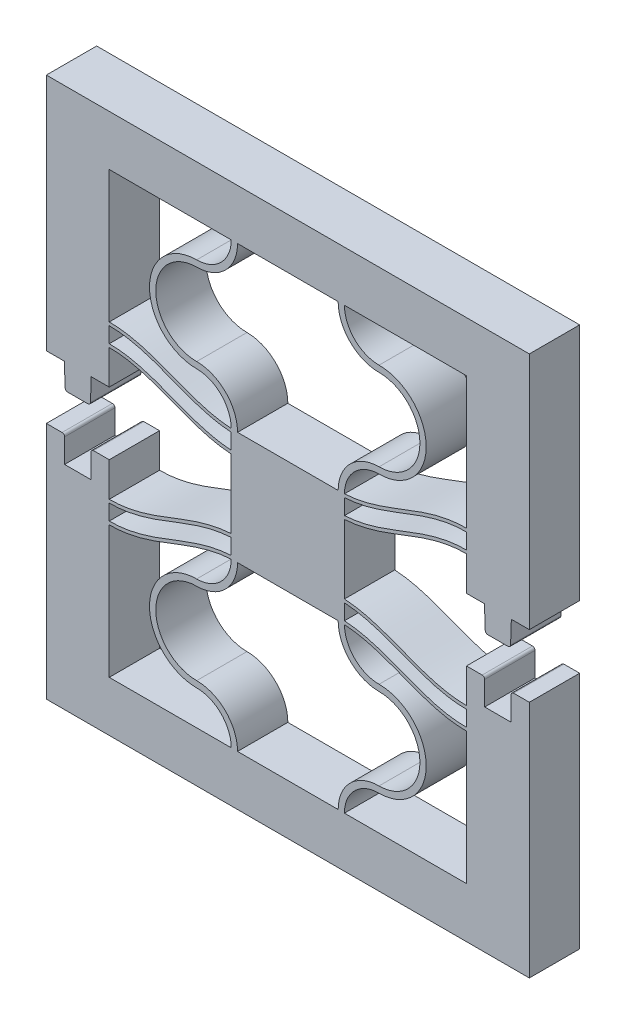
SolidWorks part; units mm, degrees
ref_plane "Front Plane" through (0, 0, 0) normal (0, 0, 1) x (1, 0, 0)
ref_plane "Top Plane" through (0, 0, 0) normal (0, 1, 0) x (1, 0, 0)
ref_plane "Right Plane" through (0, 0, 0) normal (1, 0, 0) x (0, 0, -1)
sketch "Sketch1" plane through (0, 0, 0) normal (0, 0, 1) x (1, 0, 0)
  line L4 (0, 10.5) -> (0, 0)
  line L5 (10.2, 0) -> (10.2, 13) construction
  line L6 (10.2, 13) -> (10.2, 15.9852) construction
  line L17 (9.7, 0) -> (0, 0)
  line L18 (10.7, 0) -> (20.4, 0)
  line L19 (20.4, 0) -> (20.4, 10.5)
  line L20 (10.7, 13.2452) -> (10.7, 14.4852)
  line L21 (9.7, 13.2452) -> (9.7, 14.4852)
  line L22 (10.7, 14.7452) -> (10.7, 15.9852)
  line L23 (10.7, 15.9852) -> (9.7, 15.9852)
  line L24 (9.7, 15.9852) -> (9.7, 14.7452)
  line L31 (-5, 12.26) -> (-5, -4)
  line L32 (-5, -4) -> (25.4, -4)
  line L33 (25.4, -4) -> (25.4, 12.26)
  line L34 (0, 10.76) -> (0, 12)
  line L36 (-5, 12.26) -> (0, 12.26)
  line L37 (25.4, 12.26) -> (20.4, 12.26)
  line L38 (20.4, 10.76) -> (20.4, 12)
  arc A0 (10.2, 13) -> (6.95, 9.75) centre (6.95, 13) cw
  arc A1 (6.95, 9.75) -> (6.95, 3.25) centre (6.95, 6.5) ccw
  arc A2 (6.95, 3.25) -> (10.2, 0) centre (6.95, 0) cw
  arc A3 (9.7, 12.9852) -> (6.95, 10.25) centre (6.95, 13) cw
  arc A4 (6.95, 10.25) -> (6.95, 2.75) centre (6.95, 6.5) ccw
  arc A5 (6.95, 2.75) -> (9.7, 0) centre (6.95, 0) cw
  arc A6 (9.7, 13) -> (6.95, 10.25) centre (6.95, 13) cw construction
  arc A7 (13.45, 3.25) -> (10.2, 0) centre (13.45, 0) ccw
  arc A8 (13.45, 2.75) -> (10.7, 0) centre (13.45, 0) ccw
  arc A9 (13.45, 9.75) -> (13.45, 3.25) centre (13.45, 6.5) cw
  arc A10 (13.45, 10.25) -> (13.45, 2.75) centre (13.45, 6.5) cw
  arc A11 (10.7, 12.9852) -> (13.45, 10.25) centre (13.45, 13) ccw
  arc A12 (10.2, 13) -> (13.45, 9.75) centre (13.45, 13) ccw
  spline S0 degree 4 poles (-2.0399, 10.9987) (-1.9769, 10.9844) (-1.8506, 10.9568) (-1.6594, 10.9185) (-1.4063, 10.8738) (-1.1473, 10.836) (-0.8994, 10.8056) (-0.6275, 10.7825) (-0.4084, 10.7671) (-0.0945, 10.7598) (0.0489, 10.7593) (0.3554, 10.7653) (0.5833, 10.7785) (0.8327, 10.7992) (1.1232, 10.8326) (1.4148, 10.8743) (1.7521, 10.9345) (2.2064, 11.0333) (2.726, 11.1697) (3.2397, 11.3281) (3.7479, 11.5024) (4.1845, 11.6613) (4.5513, 11.7992) (4.9172, 11.9395) (5.2828, 12.0805) (5.7402, 12.2559) (6.427, 12.5125) (7.2136, 12.7819) (8.1107, 13.0284) (9.0261, 13.1932) (9.8075, 13.2661) (10.5925, 13.2661) (11.3739, 13.1932) (12.2893, 13.0284) (13.1864, 12.7819) (13.973, 12.5125) (14.6598, 12.2559) (15.2087, 12.0455) (15.6656, 11.8688) (16.1235, 11.6948) (16.6521, 11.5024) (17.1603, 11.3281) (17.6739, 11.1697) (18.1937, 11.0333) (18.5999, 10.9449) (18.8889, 10.8915) (19.1309, 10.8534) (19.3251, 10.827) (19.5196, 10.8048) (19.7158, 10.7868) (19.909, 10.7733) (20.1017, 10.7642) (20.3513, 10.7593) (20.4943, 10.7598) (20.8085, 10.7671) (21.0274, 10.7825) (21.2994, 10.8056) (21.5473, 10.836) (21.8063, 10.8738) (22.0594, 10.9185) (22.2506, 10.9568) (22.3769, 10.9844) (22.4399, 10.9987) knots 0 0 0 0 0 0.010251 0.020502 0.030753 0.041005 0.05113 0.061255 0.071381 0.081506 0.089265 0.097024 0.112543 0.120302 0.128061 0.143579 0.159098 0.174616 0.201648 0.22868 0.244198 0.259716 0.275235 0.290753 0.306271 0.32179 0.352826 0.40689 0.437927 0.468963 0.5 0.531037 0.562073 0.59311 0.647174 0.67821 0.693729 0.709247 0.740284 0.755802 0.77132 0.798352 0.825384 0.840902 0.856421 0.86418 0.871939 0.879698 0.887457 0.895217 0.902976 0.910735 0.918494 0.928619 0.938745 0.94887 0.958995 0.969247 0.979498 0.989749 1 1 1 1 1 construction
  spline S1 degree 4 poles (0, 10.76) (0.041, 10.76) (0.1243, 10.7608) (0.3554, 10.7653) (0.5833, 10.7785) (0.8327, 10.7992) (1.1232, 10.8326) (1.4148, 10.8743) (1.7521, 10.9345) (2.2064, 11.0333) (2.726, 11.1697) (3.2397, 11.3281) (3.7479, 11.5024) (4.1845, 11.6613) (4.5513, 11.7992) (4.9172, 11.9395) (5.2828, 12.0805) (5.7402, 12.2559) (6.427, 12.5125) (7.2136, 12.7819) (8.1107, 13.0284) (9.0261, 13.1932) (9.8075, 13.2661) (10.5925, 13.2661) (11.3739, 13.1932) (12.2893, 13.0284) (13.1864, 12.7819) (13.973, 12.5125) (14.6598, 12.2559) (15.2087, 12.0455) (15.6656, 11.8688) (16.1235, 11.6948) (16.6521, 11.5024) (17.1603, 11.3281) (17.6739, 11.1697) (18.1937, 11.0333) (18.5999, 10.9449) (18.8889, 10.8915) (19.1309, 10.8534) (19.3251, 10.827) (19.5196, 10.8048) (19.7158, 10.7868) (19.909, 10.7733) (20.1017, 10.7642) (20.2757, 10.7608) (20.359, 10.76) (20.4, 10.76) knots 0.081506 0.081506 0.081506 0.081506 0.081506 0.089265 0.097024 0.112543 0.120302 0.128061 0.143579 0.159098 0.174616 0.201648 0.22868 0.244198 0.259716 0.275235 0.290753 0.306271 0.32179 0.352826 0.40689 0.437927 0.468963 0.5 0.531037 0.562073 0.59311 0.647174 0.67821 0.693729 0.709247 0.740284 0.755802 0.77132 0.798352 0.825384 0.840902 0.856421 0.86418 0.871939 0.879698 0.887457 0.895217 0.902976 0.910735 0.918494 0.918494 0.918494 0.918494 0.918494
  spline S2 degree 4 poles (-2.0399, 12.2387) (-1.9769, 12.2244) (-1.8506, 12.1968) (-1.6594, 12.1585) (-1.4063, 12.1138) (-1.1473, 12.076) (-0.8994, 12.0456) (-0.6275, 12.0225) (-0.4084, 12.0071) (-0.0945, 11.9998) (0.0489, 11.9993) (0.3554, 12.0053) (0.5833, 12.0185) (0.8327, 12.0392) (1.1232, 12.0726) (1.4148, 12.1143) (1.7521, 12.1745) (2.2064, 12.2733) (2.726, 12.4097) (3.2397, 12.5681) (3.7479, 12.7424) (4.1845, 12.9013) (4.5513, 13.0392) (4.9172, 13.1795) (5.2828, 13.3205) (5.7402, 13.4959) (6.427, 13.7525) (7.2136, 14.0219) (8.1107, 14.2684) (9.0261, 14.4332) (9.8075, 14.5061) (10.5925, 14.5061) (11.3739, 14.4332) (12.2893, 14.2684) (13.1864, 14.0219) (13.973, 13.7525) (14.6598, 13.4959) (15.2087, 13.2855) (15.6656, 13.1088) (16.1235, 12.9348) (16.6521, 12.7424) (17.1603, 12.5681) (17.6739, 12.4097) (18.1937, 12.2733) (18.5999, 12.1849) (18.8889, 12.1315) (19.1309, 12.0934) (19.3251, 12.067) (19.5196, 12.0448) (19.7158, 12.0268) (19.909, 12.0133) (20.1017, 12.0042) (20.3513, 11.9993) (20.4943, 11.9998) (20.8085, 12.0071) (21.0274, 12.0225) (21.2994, 12.0456) (21.5473, 12.076) (21.8063, 12.1138) (22.0594, 12.1585) (22.2506, 12.1968) (22.3769, 12.2244) (22.4399, 12.2387) knots 0 0 0 0 0 0.010251 0.020502 0.030753 0.041005 0.05113 0.061255 0.071381 0.081506 0.089265 0.097024 0.112543 0.120302 0.128061 0.143579 0.159098 0.174616 0.201648 0.22868 0.244198 0.259716 0.275235 0.290753 0.306271 0.32179 0.352826 0.40689 0.437927 0.468963 0.5 0.531037 0.562073 0.59311 0.647174 0.67821 0.693729 0.709247 0.740284 0.755802 0.77132 0.798352 0.825384 0.840902 0.856421 0.86418 0.871939 0.879698 0.887457 0.895217 0.902976 0.910735 0.918494 0.928619 0.938745 0.94887 0.958995 0.969247 0.979498 0.989749 1 1 1 1 1 construction
  spline S3 degree 4 poles (0, 12) (0.041, 12) (0.1243, 12.0008) (0.3554, 12.0053) (0.5833, 12.0185) (0.8327, 12.0392) (1.1232, 12.0726) (1.4148, 12.1143) (1.7521, 12.1745) (2.2064, 12.2733) (2.726, 12.4097) (3.2397, 12.5681) (3.7479, 12.7424) (4.1845, 12.9013) (4.5513, 13.0392) (4.9172, 13.1795) (5.2828, 13.3205) (5.7402, 13.4959) (6.427, 13.7525) (7.2136, 14.0219) (8.1107, 14.2684) (9.0261, 14.4332) (9.8075, 14.5061) (10.5925, 14.5061) (11.3739, 14.4332) (12.2893, 14.2684) (13.1864, 14.0219) (13.973, 13.7525) (14.6598, 13.4959) (15.2087, 13.2855) (15.6656, 13.1088) (16.1235, 12.9348) (16.6521, 12.7424) (17.1603, 12.5681) (17.6739, 12.4097) (18.1937, 12.2733) (18.5999, 12.1849) (18.8889, 12.1315) (19.1309, 12.0934) (19.3251, 12.067) (19.5196, 12.0448) (19.7158, 12.0268) (19.909, 12.0133) (20.1017, 12.0042) (20.2757, 12.0008) (20.359, 12) (20.4, 12) knots 0.081506 0.081506 0.081506 0.081506 0.081506 0.089265 0.097024 0.112543 0.120302 0.128061 0.143579 0.159098 0.174616 0.201648 0.22868 0.244198 0.259716 0.275235 0.290753 0.306271 0.32179 0.352826 0.40689 0.437927 0.468963 0.5 0.531037 0.562073 0.59311 0.647174 0.67821 0.693729 0.709247 0.740284 0.755802 0.77132 0.798352 0.825384 0.840902 0.856421 0.86418 0.871939 0.879698 0.887457 0.895217 0.902976 0.910735 0.918494 0.918494 0.918494 0.918494 0.918494
  spline S4 degree 4 poles (-2.0399, 12.4987) (-1.9769, 12.4844) (-1.8506, 12.4568) (-1.6594, 12.4185) (-1.4063, 12.3738) (-1.1473, 12.336) (-0.8994, 12.3056) (-0.6275, 12.2825) (-0.4084, 12.2671) (-0.0945, 12.2598) (0.0489, 12.2593) (0.3554, 12.2653) (0.5833, 12.2785) (0.8327, 12.2992) (1.1232, 12.3326) (1.4148, 12.3743) (1.7521, 12.4345) (2.2064, 12.5333) (2.726, 12.6697) (3.2397, 12.8281) (3.7479, 13.0024) (4.1845, 13.1613) (4.5513, 13.2992) (4.9172, 13.4395) (5.2828, 13.5805) (5.7402, 13.7559) (6.427, 14.0125) (7.2136, 14.2819) (8.1107, 14.5284) (9.0261, 14.6932) (9.8075, 14.7661) (10.5925, 14.7661) (11.3739, 14.6932) (12.2893, 14.5284) (13.1864, 14.2819) (13.973, 14.0125) (14.6598, 13.7559) (15.2087, 13.5455) (15.6656, 13.3688) (16.1235, 13.1948) (16.6521, 13.0024) (17.1603, 12.8281) (17.6739, 12.6697) (18.1937, 12.5333) (18.5999, 12.4449) (18.8889, 12.3915) (19.1309, 12.3534) (19.3251, 12.327) (19.5196, 12.3048) (19.7158, 12.2868) (19.909, 12.2733) (20.1017, 12.2642) (20.3513, 12.2593) (20.4943, 12.2598) (20.8085, 12.2671) (21.0274, 12.2825) (21.2994, 12.3056) (21.5473, 12.336) (21.8063, 12.3738) (22.0594, 12.4185) (22.2506, 12.4568) (22.3769, 12.4844) (22.4399, 12.4987) knots 0 0 0 0 0 0.010251 0.020502 0.030753 0.041005 0.05113 0.061255 0.071381 0.081506 0.089265 0.097024 0.112543 0.120302 0.128061 0.143579 0.159098 0.174616 0.201648 0.22868 0.244198 0.259716 0.275235 0.290753 0.306271 0.32179 0.352826 0.40689 0.437927 0.468963 0.5 0.531037 0.562073 0.59311 0.647174 0.67821 0.693729 0.709247 0.740284 0.755802 0.77132 0.798352 0.825384 0.840902 0.856421 0.86418 0.871939 0.879698 0.887457 0.895217 0.902976 0.910735 0.918494 0.928619 0.938745 0.94887 0.958995 0.969247 0.979498 0.989749 1 1 1 1 1 construction
  spline S5 degree 4 poles (0, 12.26) (0.041, 12.26) (0.1243, 12.2608) (0.3554, 12.2653) (0.5833, 12.2785) (0.8327, 12.2992) (1.1232, 12.3326) (1.4148, 12.3743) (1.7521, 12.4345) (2.2064, 12.5333) (2.726, 12.6697) (3.2397, 12.8281) (3.7479, 13.0024) (4.1845, 13.1613) (4.5513, 13.2992) (4.9172, 13.4395) (5.2828, 13.5805) (5.7402, 13.7559) (6.427, 14.0125) (7.2136, 14.2819) (8.1107, 14.5284) (9.0261, 14.6932) (9.8075, 14.7661) (10.5925, 14.7661) (11.3739, 14.6932) (12.2893, 14.5284) (13.1864, 14.2819) (13.973, 14.0125) (14.6598, 13.7559) (15.2087, 13.5455) (15.6656, 13.3688) (16.1235, 13.1948) (16.6521, 13.0024) (17.1603, 12.8281) (17.6739, 12.6697) (18.1937, 12.5333) (18.5999, 12.4449) (18.8889, 12.3915) (19.1309, 12.3534) (19.3251, 12.327) (19.5196, 12.3048) (19.7158, 12.2868) (19.909, 12.2733) (20.1017, 12.2642) (20.2757, 12.2608) (20.359, 12.26) (20.4, 12.26) knots 0.081506 0.081506 0.081506 0.081506 0.081506 0.089265 0.097024 0.112543 0.120302 0.128061 0.143579 0.159098 0.174616 0.201648 0.22868 0.244198 0.259716 0.275235 0.290753 0.306271 0.32179 0.352826 0.40689 0.437927 0.468963 0.5 0.531037 0.562073 0.59311 0.647174 0.67821 0.693729 0.709247 0.740284 0.755802 0.77132 0.798352 0.825384 0.840902 0.856421 0.86418 0.871939 0.879698 0.887457 0.895217 0.902976 0.910735 0.918494 0.918494 0.918494 0.918494 0.918494
  spline S8 degree 4 poles (-2.0399, 10.7387) (-1.9769, 10.7244) (-1.8506, 10.6968) (-1.6594, 10.6585) (-1.4063, 10.6138) (-1.1473, 10.576) (-0.8994, 10.5456) (-0.6275, 10.5225) (-0.4084, 10.5071) (-0.0945, 10.4998) (0.0489, 10.4993) (0.3554, 10.5053) (0.5833, 10.5185) (0.8327, 10.5392) (1.1232, 10.5726) (1.4148, 10.6143) (1.7521, 10.6745) (2.2064, 10.7733) (2.726, 10.9097) (3.2397, 11.0681) (3.7479, 11.2424) (4.1845, 11.4013) (4.5513, 11.5392) (4.9172, 11.6795) (5.2828, 11.8205) (5.7402, 11.9959) (6.427, 12.2525) (7.2136, 12.5219) (8.1107, 12.7684) (9.0261, 12.9332) (9.8075, 13.0061) (10.5925, 13.0061) (11.3739, 12.9332) (12.2893, 12.7684) (13.1864, 12.5219) (13.973, 12.2525) (14.6598, 11.9959) (15.2087, 11.7855) (15.6656, 11.6088) (16.1235, 11.4348) (16.6521, 11.2424) (17.1603, 11.0681) (17.6739, 10.9097) (18.1937, 10.7733) (18.5999, 10.6849) (18.8889, 10.6315) (19.1309, 10.5934) (19.3251, 10.567) (19.5196, 10.5448) (19.7158, 10.5268) (19.909, 10.5133) (20.1017, 10.5042) (20.3513, 10.4993) (20.4943, 10.4998) (20.8085, 10.5071) (21.0274, 10.5225) (21.2994, 10.5456) (21.5473, 10.576) (21.8063, 10.6138) (22.0594, 10.6585) (22.2506, 10.6968) (22.3769, 10.7244) (22.4399, 10.7387) knots 0 0 0 0 0 0.010251 0.020502 0.030753 0.041005 0.05113 0.061255 0.071381 0.081506 0.089265 0.097024 0.112543 0.120302 0.128061 0.143579 0.159098 0.174616 0.201648 0.22868 0.244198 0.259716 0.275235 0.290753 0.306271 0.32179 0.352826 0.40689 0.437927 0.468963 0.5 0.531037 0.562073 0.59311 0.647174 0.67821 0.693729 0.709247 0.740284 0.755802 0.77132 0.798352 0.825384 0.840902 0.856421 0.86418 0.871939 0.879698 0.887457 0.895217 0.902976 0.910735 0.918494 0.928619 0.938745 0.94887 0.958995 0.969247 0.979498 0.989749 1 1 1 1 1 construction
  spline S9 degree 4 poles (0, 10.5) (0.041, 10.5) (0.1243, 10.5008) (0.3554, 10.5053) (0.5833, 10.5185) (0.8327, 10.5392) (1.1232, 10.5726) (1.4148, 10.6143) (1.7521, 10.6745) (2.2064, 10.7733) (2.726, 10.9097) (3.2397, 11.0681) (3.7479, 11.2424) (4.1845, 11.4013) (4.5513, 11.5392) (4.9172, 11.6795) (5.2828, 11.8205) (5.7402, 11.9959) (6.427, 12.2525) (7.2136, 12.5219) (8.1107, 12.7684) (9.0261, 12.9332) (9.8075, 13.0061) (10.5925, 13.0061) (11.3739, 12.9332) (12.2893, 12.7684) (13.1864, 12.5219) (13.973, 12.2525) (14.6598, 11.9959) (15.2087, 11.7855) (15.6656, 11.6088) (16.1235, 11.4348) (16.6521, 11.2424) (17.1603, 11.0681) (17.6739, 10.9097) (18.1937, 10.7733) (18.5999, 10.6849) (18.8889, 10.6315) (19.1309, 10.5934) (19.3251, 10.567) (19.5196, 10.5448) (19.7158, 10.5268) (19.909, 10.5133) (20.1017, 10.5042) (20.2757, 10.5008) (20.359, 10.5) (20.4, 10.5) knots 0.081506 0.081506 0.081506 0.081506 0.081506 0.089265 0.097024 0.112543 0.120302 0.128061 0.143579 0.159098 0.174616 0.201648 0.22868 0.244198 0.259716 0.275235 0.290753 0.306271 0.32179 0.352826 0.40689 0.437927 0.468963 0.5 0.531037 0.562073 0.59311 0.647174 0.67821 0.693729 0.709247 0.740284 0.755802 0.77132 0.798352 0.825384 0.840902 0.856421 0.86418 0.871939 0.879698 0.887457 0.895217 0.902976 0.910735 0.918494 0.918494 0.918494 0.918494 0.918494
  dimension "D4" = 0.26
  dimension "D6" = 4
  dimension "D1" = 13
  dimension "D2" = 0.5
  dimension "D3" = 0.26
  dimension "D7" = 5
  dimension "D5" = 1.5
extrude "Boss-Extrude1" add sketch "Sketch1" along normal blind 4
sketch "Sketch4" plane through (0, 15.9852, 0) normal (0, 1, 0) x (1, 0, 0)
  line L24 (10.7, 0) -> (9.7, 0)
  line L25 (9.7, 0) -> (9.7, -4)
  line L26 (10.7, 0) -> (9.7, 0)
  line L27 (10.7, -4) -> (10.7, 0)
  line L29 (9.7, 0) -> (9.7, -4)
  line L31 (10.7, -4) -> (10.7, 0)
  line L32 (9.7, -4) -> (10.7, -4)
  line L33 (9.7, -4) -> (10.7, -4)
  dimension "D1" = 0
extrude "Boss-Extrude2" add sketch "Sketch4" along normal blind 1.5
mirror "Mirror3" about plane through (0, 17.4852, 0) normal (0, 1, 0) of bodies 179
ref_plane "Plane1" through (10.2, 0, 0) normal (-1, 0, 0) x (0, 0, 1)
split "Split2" trim tools "Plane1" bodies to split 247 102 resulting bodies 225
sketch "Sketch7" plane through (10.2, 0, 0) normal (-1, 0, 0) x (0, 0, 1)
  line L4 (4, 34.9704) -> (4, 38.9704)
  line L12 (0, 13) -> (4, 13)
  line L13 (0, 13) -> (4, 13)
  line L14 (4, 13) -> (4, 21.9704)
  line L15 (4, 13) -> (4, 21.9704)
  line L20 (4, 0) -> (0, 0)
  line L22 (4, 0) -> (0, 0)
  line L23 (0, -4) -> (4, -4)
  line L27 (0, -4) -> (4, -4)
  line L31 (4, 21.9704) -> (0, 21.9704)
  line L32 (4, 21.9704) -> (0, 21.9704)
  line L33 (0, 21.9704) -> (0, 13)
  line L34 (0, 21.9704) -> (0, 13)
  line L36 (4, -4) -> (4, 0)
  line L38 (4, 34.9704) -> (4, 38.9704)
  line L39 (4, 34.9704) -> (4, 38.9704)
  line L40 (4, 38.9704) -> (0, 38.9704)
  line L41 (4, 38.9704) -> (0, 38.9704)
  line L46 (4, 34.9704) -> (4, 38.9704)
  line L51 (0, 38.9704) -> (0, 34.9704)
  line L52 (0, 38.9704) -> (0, 34.9704)
  line L53 (0, 34.9704) -> (4, 34.9704)
  line L54 (0, 34.9704) -> (4, 34.9704)
  line L55 (4, 38.9704) -> (0, 38.9704)
  line L57 (4, 38.9704) -> (0, 38.9704)
  line L59 (4, -4) -> (4, 0)
  line L60 (0, 0) -> (0, -4)
  line L61 (0, 0) -> (0, -4)
  line L62 (0, 38.9704) -> (0, 34.9704)
  line L63 (0, 38.9704) -> (0, 34.9704)
  line L64 (0, 34.9704) -> (4, 34.9704)
  line L65 (0, 34.9704) -> (4, 34.9704)
  dimension "D1" = 0
  dimension "D2" = 0
  dimension "D3" = 0
  dimension "D4" = 0
extrude "Boss-Extrude3" add sketch "Sketch7" along normal blind 4
mirror "Mirror2" about plane through (6.2, 0, 0) normal (-1, 0, 0) of bodies 226
sketch "Sketch8" plane through (0, 0, 4) normal (0, 0, 1) x (1, 0, 0)
  line L0 (20.4, 0) -> (20.4, 10.5) construction
  line L1 (-13, 22.7104) -> (-8, 22.7104)
  line L2 (-13, 22.7104) -> (-13, 19.9852)
  line L3 (-13, 19.9852) -> (-8, 19.9852)
  line L4 (-8, 22.7104) -> (-8, 19.9852)
  line L5 (-13, 12.26) -> (-8, 12.26)
  line L6 (-13, 12.26) -> (-13, 14.9852)
  line L7 (-13, 14.9852) -> (-8, 14.9852)
  line L8 (-8, 12.26) -> (-8, 14.9852)
  line L9 (25.4, 12.26) -> (20.4, 12.26)
  line L10 (25.4, 12.26) -> (25.4, 14.9852)
  line L11 (25.4, 14.9852) -> (20.4, 14.9852)
  line L12 (20.4, 12.26) -> (20.4, 14.9852)
  line L13 (20.4, 22.7104) -> (25.4, 22.7104)
  line L14 (20.4, 22.7104) -> (20.4, 19.9852)
  line L15 (20.4, 19.9852) -> (25.4, 19.9852)
  line L16 (25.4, 22.7104) -> (25.4, 19.9852)
  line L17 (25.4, 38.9704) -> (25.4, 22.7104) construction
  line L18 (-8, 0) -> (-8, 10.5) construction
  line L19 (-8, 34.9704) -> (-8, 24.4704) construction
  dimension "D1" = 5
extrude "Boss-Extrude4" add sketch "Sketch8" against normal up to surface (4 mm away) up to face at (6.2, 17.4852, 0)
sketch "Sketch9" plane through (0, 0, 4) normal (0, 0, 1) x (1, 0, 0)
  line L0 (-13, 19.9852) -> (-8, 19.9852) construction
  line L1 (-9.5, 19.9852) -> (-11.5, 19.9852)
  line L2 (-9.5, 19.9852) -> (-9.5, 17.9852)
  line L3 (-9.5, 17.9852) -> (-11.5, 17.9852)
  line L4 (-11.5, 19.9852) -> (-11.5, 17.9852)
  line L5 (20.4, 19.9852) -> (25.4, 19.9852) construction
  line L6 (21.9, 19.9852) -> (23.9, 19.9852)
  line L7 (21.9, 19.9852) -> (21.9, 17.9852)
  line L8 (21.9, 17.9852) -> (23.9, 17.9852)
  line L9 (23.9, 19.9852) -> (23.9, 17.9852)
  point P12 (-10.5, 19.9852)
  point P13 (22.9, 19.9852)
  point P14 (22.9, 19.9852)
  dimension "D1" = 2
  dimension "D2" = 2
extrude "Boss-Extrude5" add sketch "Sketch9" against normal up to surface (4 mm away) up to face at (6.2, 17.4852, 0)
sketch "Sketch10" plane through (0, 0, 4) normal (0, 0, 1) x (1, 0, 0)
  line L0 (-8, 14.9852) -> (-13, 14.9852) construction
  line L1 (-9.45, 14.9852) -> (-11.55, 14.9852)
  line L2 (-9.45, 14.9852) -> (-9.45, 12.8852)
  line L3 (-9.45, 12.8852) -> (-11.55, 12.8852)
  line L4 (-11.55, 14.9852) -> (-11.55, 12.8852)
  line L5 (25.4, 14.9852) -> (20.4, 14.9852) construction
  line L6 (21.85, 14.9852) -> (23.95, 14.9852)
  line L7 (21.85, 14.9852) -> (21.85, 12.8852)
  line L8 (21.85, 12.8852) -> (23.95, 12.8852)
  line L9 (23.95, 14.9852) -> (23.95, 12.8852)
  point P12 (-10.5, 14.9852)
  point P13 (-10.5, 14.9852)
  point P14 (22.9, 14.9852)
  point P15 (22.9, 14.9852)
  dimension "D1" = 2.1
  dimension "D2" = 2.1
extrude "Cut-Extrude1" cut sketch "Sketch10" against normal up to surface (4 mm away) up to face at (6.2, 17.9138, 0)
draft "Draft1" type of draft neutral plane draft angle 2 faces to draft 4 face at (23.9, 18.9852, 2) face at (21.9, 18.9852, 2) face at (-9.5, 18.9852, 2) face at (-11.5, 18.9852, 2) neutral plane through (-9.5, 17.9852, -2.8284) neutral plane normal (0, -1, 0) parameters "D1"=2
fillet "Fillet1" radius 0.2 8 edges at (21.9, 17.9852, 2) (23.9, 17.9852, 2) (21.85, 14.9852, 2) (23.95, 14.9852, 2) (-9.5, 17.9852, 2) (-11.5, 17.9852, 2) (-9.45, 14.9852, 2) (-11.55, 14.9852, 2)
